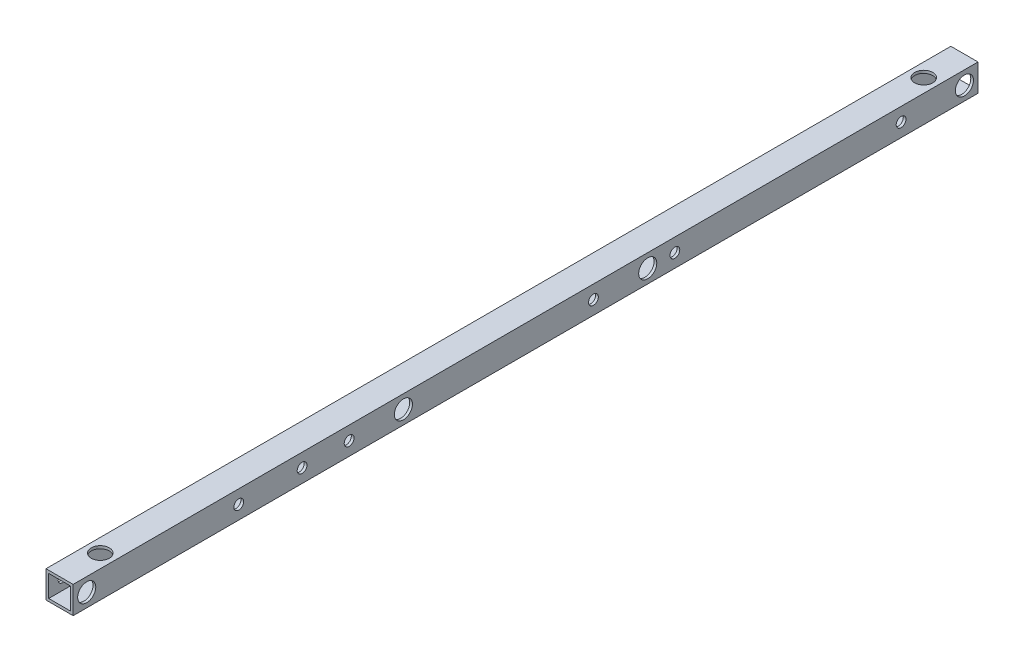
SolidWorks part; units mm, degrees
material "6063-T5"
ref_plane "正面" through (0, 0, 0) normal (0, 0, 1) x (1, 0, 0)
ref_plane "平面" through (0, 0, 0) normal (0, 1, 0) x (1, 0, 0)
ref_plane "右側面" through (0, 0, 0) normal (1, 0, 0) x (0, 0, -1)
sketch "ｽｹｯﾁ1" plane through (0, 0, 0) normal (0, 0, 1) x (1, 0, 0)
  line L1 (-7.5, -7.5) -> (7.5, -7.5)
  line L2 (-7.5, -7.5) -> (-7.5, 7.5)
  line L3 (-7.5, 7.5) -> (7.5, 7.5)
  line L4 (7.5, -7.5) -> (7.5, 7.5)
  line L5 (-7.5, -7.5) -> (7.5, 7.5) construction
  line L6 (-7.5, 7.5) -> (7.5, -7.5) construction
  line L7 (-6, -6) -> (6, -6)
  line L8 (-6, -6) -> (-6, 6)
  line L9 (-6, 6) -> (6, 6)
  line L10 (6, -6) -> (6, 6)
  line L11 (-6, -6) -> (6, 6) construction
  line L12 (-6, 6) -> (6, -6) construction
  point P0 (0, 0)
  point P6 (0, 0)
  dimension "D1" = 1.5
  dimension "D2" = 15
  dimension "D3" = 15
extrude "ﾎﾞｽ - 押し出し1" add sketch "ｽｹｯﾁ1" along normal blind 500
sketch "ｽｹｯﾁ2" plane through (7.5, 0, 0) normal (1, 0, 0) x (0, 0, -1)
  line L0 (-500, -7.5) -> (0, -7.5) construction
  line L1 (0, -7.5) -> (0, 7.5) construction
  line L2 (-500, -7.5) -> (-500, 7.5) construction
  line L3 (-500, 7.5) -> (0, 7.5) construction
  circle A4 centre (-492.5, 0) radius 2.25
  circle A8 centre (-7.5, 0) radius 2.25
  circle A9 centre (-317.5, 0) radius 2.25
  circle A10 centre (-182.5, 0) radius 2.25
  point P16 (-250, 7.5)
  dimension "D1" = 4.5
  dimension "D2" = 7.5
  dimension "D3" = 7.5
  dimension "D6" = 67.5
  dimension "D7" = 2
  dimension "D8" = 135
  dimension "D4" = 7.5
  dimension "D9" = 2
  dimension "D5" = 2
extrude "ｶｯﾄ - 押し出し1" cut sketch "ｽｹｯﾁ2" against normal blind 25
sketch "ｽｹｯﾁ4" plane through (0, -7.5, 0) normal (0, -1, 0) x (-1, 0, 0)
  line L2 (7.5, 0) -> (-7.5, 0) construction
  line L3 (-7.5, -500) -> (-7.5, 0) construction
  line L4 (7.5, -500) -> (-7.5, -500) construction
  line L5 (7.5, -500) -> (7.5, 0) construction
  circle A2 centre (0, -22.5) radius 2.25
  circle A3 centre (0, -477.5) radius 2.25
  dimension "D1" = 22.5
  dimension "D2" = 4.5
  dimension "D3" = 7.5
  dimension "D6" = 4.5
  dimension "D8" = 22.5
  dimension "D4" = 7.5
extrude "ｶｯﾄ - 押し出し3" cut sketch "ｽｹｯﾁ4" against normal blind 20
sketch "ｽｹｯﾁ5" plane through (7.5, 0, 0) normal (1, 0, 0) x (0, 0, -1)
  circle A0 centre (-492.5, 0) radius 5
  circle A1 centre (-7.5, 0) radius 5
  circle A2 centre (-182.5, 0) radius 5
  circle A3 centre (-317.5, 0) radius 5
  dimension "D1" = 10
  dimension "D2" = 10
  dimension "D3" = 10
  dimension "D4" = 10
extrude "ｶｯﾄ - 押し出し4" cut sketch "ｽｹｯﾁ5" against normal blind 3.3
sketch "ｽｹｯﾁ6" plane through (0, 7.5, 0) normal (0, 1, 0) x (1, 0, 0)
  circle A0 centre (0, -22.5) radius 5
  circle A2 centre (0, -477.5) radius 5
  dimension "D2" = 10
  dimension "D3" = 10
extrude "ｶｯﾄ - 押し出し5" cut sketch "ｽｹｯﾁ6" against normal blind 3.3
sketch "ｽｹｯﾁ7" plane through (7.5, 0, 0) normal (1, 0, 0) x (0, 0, -1)
  line L0 (-500, -7.5) -> (-500, 7.5) construction
  circle A0 centre (-317.5, 0) radius 5 construction
  circle A1 centre (-182.5, 0) radius 5 construction
  point P0 (-347.5, 0)
  point P1 (-212.5, 0)
  point P6 (-500, 0)
  point P7 (-167.5, 0)
  point P9 (-42.5, 0)
  point P14 (-373.5, 0)
  point P16 (-408.5, 0)
  dimension "D2" = 30
  dimension "D1" = 135
  dimension "D3" = 125
  dimension "D4" = 15
  dimension "D5" = 35
  dimension "D6" = 26
hole_wizard "Ø5.4 (5.4) 直径の穴1" positions "ｽｹｯﾁ7" profile "ｽｹｯﾁ8" hole size "Ø5.4" standard "JIS" end condition through all
sketch "ｽｹｯﾁ8" plane through (7.5, 0, 347.5) normal (0, 1, 0) x (0, 0, -1)
  line L0 (0, 0) -> (0, 15)
  line L1 (0, 15) -> (2.7, 15)
  line L2 (2.7, 15) -> (2.7, 0)
  line L5 (2.7, 0) -> (0, 0)
  line L11 (0, -6.35) -> (0, 107.95) construction
  dimension "通し穴の直径" = 5.4
  dimension "通し穴の深さ" = 15
hole_wizard "Ø10.0 (10) 直径の穴1" positions "ｽｹｯﾁ9" profile "ｽｹｯﾁ10" hole size "Ø10.0" standard "JIS"
sketch "ｽｹｯﾁ9" plane through (-7.5, 0, 0) normal (-1, 0, 0) x (0, 0, 1)
  point P0 (347.5, 0)
  point P3 (212.5, 0)
  point P6 (167.5, 0)
  point P9 (42.5, 0)
  point P13 (373.5, 0)
  point P16 (408.5, 0)
sketch "ｽｹｯﾁ10" plane through (-7.5, 0, 347.5) normal (0, 1, 0) x (0, 0, 1)
  line L0 (0, 0) -> (0, 4.5043)
  line L1 (0, 4.5043) -> (5, 1.5)
  line L2 (5, 1.5) -> (5, 0)
  line L5 (5, 0) -> (0, 0)
  line L10 (0, 4.5043) -> (-5, 1.5) construction
  line L11 (0, -6.35) -> (0, 107.95) construction
  dimension "穴の直径" = 10
  dimension "穴の深さ" = 1.5
  dimension "ﾄﾞﾘﾙ角度" = 118
